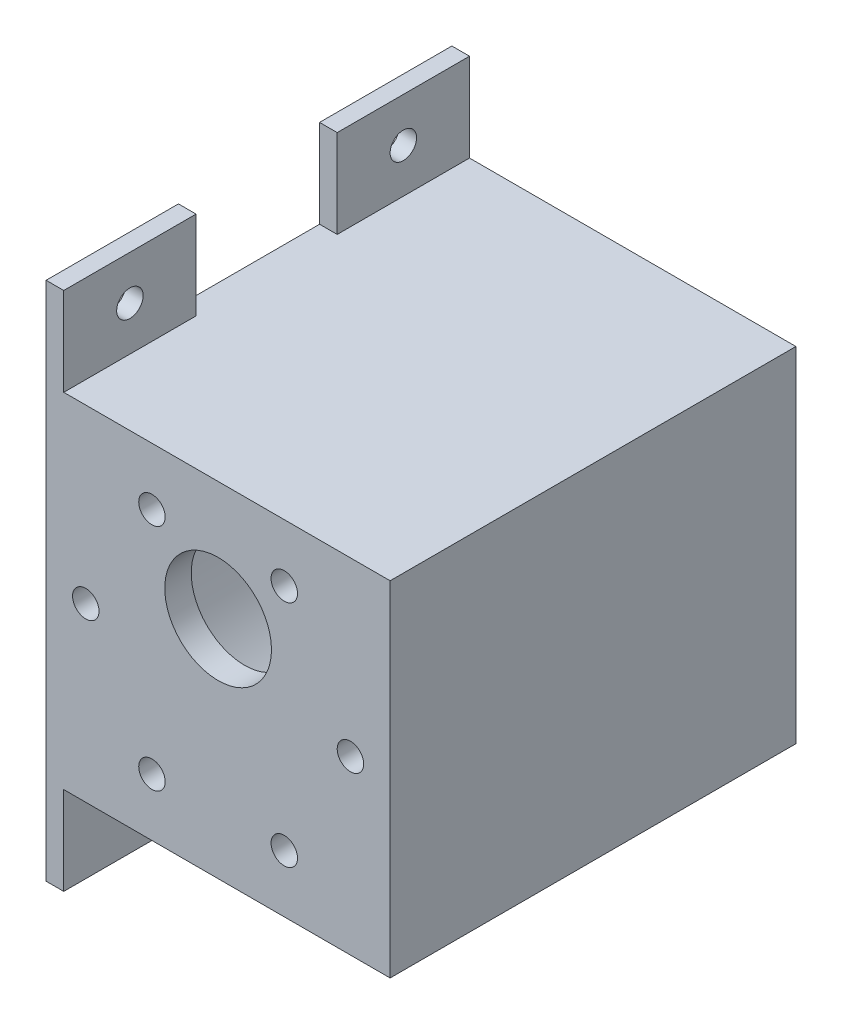
SolidWorks part; units mm, degrees
ref_plane "Front Plane" through (0, 0, 0) normal (0, 0, 1) x (1, 0, 0)
ref_plane "Top Plane" through (0, 0, 0) normal (0, 1, 0) x (1, 0, 0)
ref_plane "Right Plane" through (0, 0, 0) normal (1, 0, 0) x (0, 0, -1)
sketch "Sketch1" plane through (0, 0, 0) normal (0, 0, 1) x (1, 0, 0)
  circle A0 centre (0, 0) radius 18.05
  dimension "D1" = 36.1
extrude "Boss-Extrude1" add sketch "Sketch1" along normal blind 3
sketch "Sketch2" plane through (0, 0, 3) normal (0, 0, 1) x (1, 0, 0)
  line L0 (-27.7311, 0) -> (35.8282, 0) construction
  line L1 (0, 19.3831) -> (0, -20.9595) construction
  circle A0 centre (-15, 0) radius 1.5
  dimension "D2" = 3
  dimension "D1" = 15
extrude "Cut-Extrude1" cut sketch "Sketch2" against normal blind 3
pattern_circular "CirPattern1" count 6 over 360 about axis through (0, 0, 0) along (0, 0, 1) of "Cut-Extrude1"
sketch "Sketch3" plane through (0, 0, 3) normal (0, 0, 1) x (1, 0, 0)
  circle A0 centre (0, 6) radius 6.05
  dimension "D2" = 12.1
  dimension "D1" = 6
extrude "Cut-Extrude2" cut sketch "Sketch3" against normal blind 3
sketch "Sketch4" plane through (0, 0, 3) normal (0, 0, 1) x (1, 0, 0)
  line L1 (-19.5, -19.5) -> (19.5, -19.5)
  line L2 (-19.5, -19.5) -> (-19.5, 19.5)
  line L3 (-19.5, 19.5) -> (19.5, 19.5)
  line L4 (19.5, -19.5) -> (19.5, 19.5)
  line L5 (-19.5, -19.5) -> (19.5, 19.5) construction
  line L6 (-19.5, 19.5) -> (19.5, -19.5) construction
  circle A0 centre (0, 0) radius 18.05 construction
  circle A1 centre (0, 0) radius 18.05
  point P0 (0, 0)
  dimension "D1" = 39
  dimension "D2" = 39
extrude "Boss-Extrude2" add sketch "Sketch4" against normal blind 21
sketch "Sketch5" plane through (0, 0, -18) normal (0, 0, -1) x (-1, 0, 0)
  line L0 (0, 18.05) -> (19.5, 18.05)
  line L1 (19.5, 19.5) -> (19.5, -19.5) construction
  line L2 (19.5, 18.05) -> (19.5, 19.5)
  line L3 (0, -18.05) -> (19.5, -18.05)
  line L4 (19.5, -18.05) -> (19.5, -19.5)
  line L5 (-19.5, -19.5) -> (-19.5, 19.5) construction
  line L6 (-19.5, 19.5) -> (19.5, 19.5) construction
  line L7 (19.5, -19.5) -> (-19.5, -19.5) construction
  line L8 (-19.5, -19.5) -> (-19.5, 19.5)
  line L9 (-19.5, 19.5) -> (19.5, 19.5)
  line L10 (19.5, -19.5) -> (-19.5, -19.5)
  circle A0 centre (0, 0) radius 18.05 construction
  arc A1 (0, 18.05) -> (0, -18.05) centre (0, 0) ccw
extrude "Boss-Extrude3" add sketch "Sketch5" along normal blind 25
sketch "Sketch6" plane through (-19.5, 0, 0) normal (-1, 0, 0) x (0, 0, 1)
  line L0 (-43, 19.5) -> (-43, 29.5)
  line L1 (-28, 19.5) -> (-28, 29.5)
  line L2 (-43, 19.5) -> (3, 19.5) construction
  line L3 (-28, 29.5) -> (-43, 29.5)
  line L4 (-68.7562, 0) -> (30.09, 0) construction
  line L5 (-28, -19.5) -> (-28, -29.5)
  line L6 (-28, -29.5) -> (-43, -29.5)
  line L7 (-43, -19.5) -> (-43, -29.5)
  line L8 (-43, 19.5) -> (-28, 19.5)
  line L9 (-43, -19.5) -> (-28, -19.5)
  circle A0 centre (-35.5, 24.5) radius 1.5
  circle A1 centre (-35.5, -24.5) radius 1.5
  dimension "D3" = 3
  dimension "D1" = 10
  dimension "D2" = 15
  dimension "D4" = 7.5
  dimension "D5" = 5
extrude "Boss-Extrude4" add sketch "Sketch6" against normal blind 2
sketch "Sketch7" plane through (-19.5, 0, 0) normal (-1, 0, 0) x (0, 0, 1)
  line L0 (3, 19.5) -> (3, 29.5)
  line L1 (3, 29.5) -> (-12, 29.5)
  line L2 (-12, 29.5) -> (-12, 19.5)
  line L3 (-28, 19.5) -> (3, 19.5) construction
  line L4 (-12, 19.5) -> (3, 19.5)
  line L5 (-57.6553, 0) -> (45.3241, 0) construction
  line L6 (-12, -29.5) -> (-12, -19.5)
  line L7 (-12, -19.5) -> (3, -19.5)
  line L8 (3, -19.5) -> (3, -29.5)
  line L9 (3, -29.5) -> (-12, -29.5)
  circle A0 centre (-4.5, 24.5) radius 1.5
  circle A1 centre (-4.5, -24.5) radius 1.5
  dimension "D5" = 3
  dimension "D1" = 10
  dimension "D2" = 15
  dimension "D3" = 5
  dimension "D4" = 7.5
extrude "Boss-Extrude5" add sketch "Sketch7" against normal blind 2
